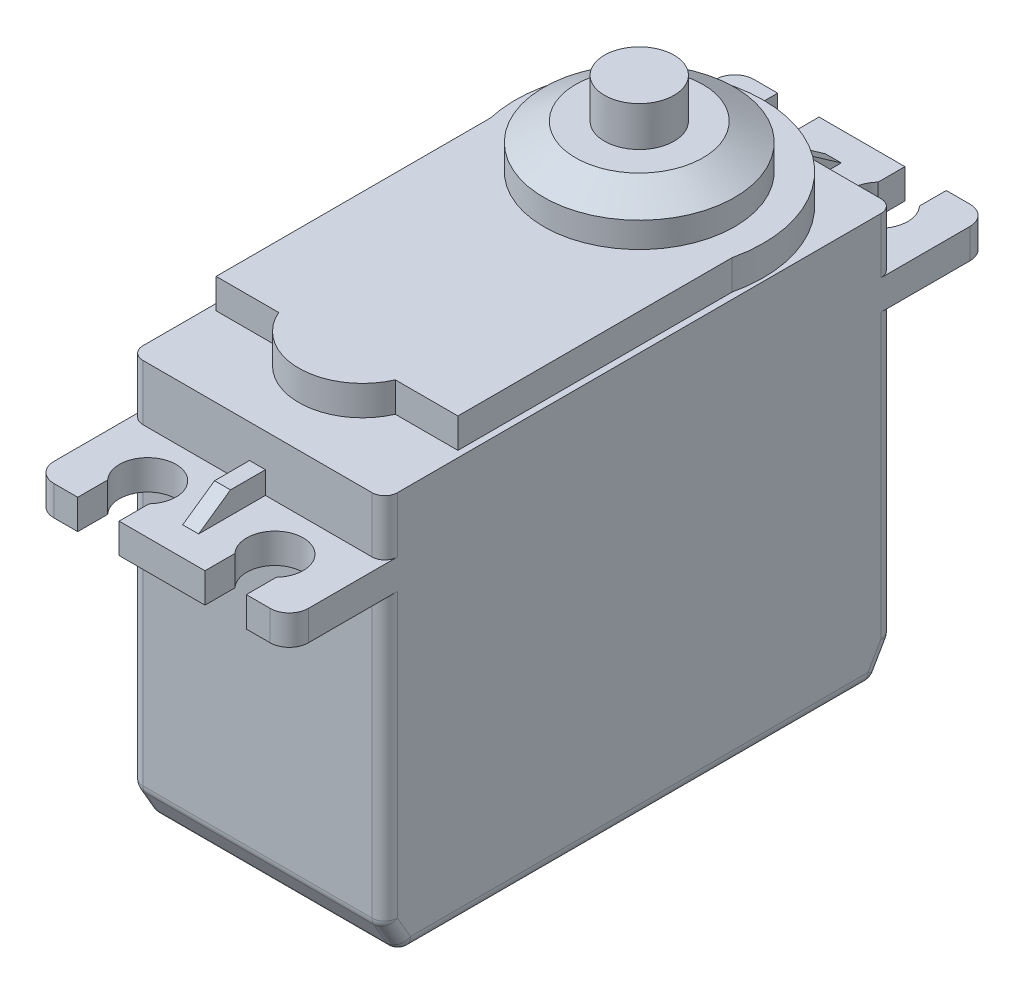
SolidWorks part; units mm, degrees
ref_plane "Front Plane" through (0, 0, 0) normal (0, 0, 1) x (1, 0, 0)
ref_plane "Top Plane" through (0, 0, 0) normal (0, 1, 0) x (1, 0, 0)
ref_plane "Right Plane" through (0, 0, 0) normal (1, 0, 0) x (0, 0, -1)
sketch "Sketch1" plane through (0, 0, 0) normal (0, 1, 0) x (1, 0, 0)
  line L1 (-10.16, 10.16) -> (10.16, 10.16)
  line L2 (-10.16, 10.16) -> (-10.16, -30.48)
  line L3 (-10.16, -30.48) -> (10.16, -30.48)
  line L4 (10.16, 10.16) -> (10.16, -30.48)
  dimension "D1" = 20.32
  dimension "D2" = 40.64
  dimension "D3" = 10.16
  dimension "D4" = 10.16
extrude "Extrude1" add sketch "Sketch1" along normal blind 25.4
sketch "Sketch2" plane through (0, 25.4, 0) normal (0, 1, 0) x (-1, 0, 0)
  line L0 (10.16, 30.48) -> (10.16, 38.1)
  line L1 (10.16, 38.1) -> (6.731, 38.1)
  line L2 (-10.16, 38.1) -> (-10.16, 30.48)
  line L3 (10.16, -10.16) -> (10.16, -17.78)
  line L4 (10.16, -10.16) -> (10.16, 30.48)
  line L5 (10.16, 30.48) -> (-10.16, 30.48)
  line L6 (-10.16, 30.48) -> (-10.16, -10.16)
  line L7 (-10.16, -10.16) -> (10.16, -10.16)
  line L8 (10.16, -10.16) -> (10.16, 30.48)
  line L9 (10.16, 30.48) -> (-10.16, 30.48)
  line L10 (-10.16, 30.48) -> (-10.16, -10.16)
  line L11 (-10.16, -10.16) -> (10.16, -10.16)
  line L12 (10.16, -17.78) -> (6.731, -17.78)
  line L13 (-10.16, -17.78) -> (-10.16, -10.16)
  line L14 (-6.731, 35.7072) -> (-6.731, 38.1)
  line L15 (-3.429, 35.7072) -> (-3.429, 38.1)
  line L16 (3.429, 35.7072) -> (3.429, 38.1)
  line L17 (6.731, 35.7072) -> (6.731, 38.1)
  line L18 (6.731, -15.6412) -> (6.731, -17.78)
  line L19 (3.429, -15.6412) -> (3.429, -17.78)
  line L20 (-3.429, -15.6412) -> (-3.429, -17.78)
  line L21 (-6.731, -15.6412) -> (-6.731, -17.78)
  line L22 (-6.731, -17.78) -> (-10.16, -17.78)
  line L23 (3.429, -17.78) -> (-3.429, -17.78)
  line L24 (-6.731, 38.1) -> (-10.16, 38.1)
  line L25 (3.429, 38.1) -> (-3.429, 38.1)
  arc A0 (3.429, 35.7072) -> (6.731, 35.7072) centre (5.08, 34.163) ccw
  arc A1 (-6.731, 35.7072) -> (-3.429, 35.7072) centre (-5.08, 34.163) ccw
  arc A2 (-3.429, -15.6412) -> (-6.731, -15.6412) centre (-5.08, -14.097) ccw
  arc A3 (6.731, -15.6412) -> (3.429, -15.6412) centre (5.08, -14.097) ccw
  line M5 (10.16, -10.16) -> (10.16, 30.48)
  line M6 (10.16, 30.48) -> (-10.16, 30.48)
  line M7 (-10.16, 30.48) -> (-10.16, -10.16)
  line M8 (-10.16, -10.16) -> (10.16, -10.16)
  dimension "D2" = 4.5212
  dimension "D9" = 3.302
  dimension "D3" = 5.08
  dimension "D4" = 10.16
  dimension "D5" = 48.26
  dimension "D6" = 3.937
  dimension "D7" = 7.62
  dimension "D8" = 7.62
  dimension "D10" = 3.302
  dimension "D11" = 1.651
  dimension "D12" = 1.651
  dimension "D1" = 0
extrude "Extrude2" add sketch "Sketch2" along normal blind 2.3813 contours M8 M5 M6 M7 | A3 L18 L12 L3 L13 L22 L21 A2 L20 L23 L19 M8 | A1 L14 L24 L2 L0 L1 L17 A0 L16 L25 L15 M6
sketch "Sketch3" plane through (0, 27.7812, 0) normal (0, 1, 0) x (-1, 0, 0)
  line L4 (10.16, -10.16) -> (10.16, 30.48)
  line L5 (-10.16, -10.16) -> (10.16, -10.16)
  line L6 (-10.16, 30.48) -> (-10.16, -10.16)
  line L7 (10.16, 30.48) -> (-10.16, 30.48)
  line L8 (10.16, -10.16) -> (10.16, 30.48)
  line L9 (-10.16, -10.16) -> (10.16, -10.16)
  line L10 (-10.16, 30.48) -> (-10.16, -10.16)
  line L11 (10.16, 30.48) -> (-10.16, 30.48)
  dimension "D1" = 0
extrude "Extrude3" add sketch "Sketch3" along normal blind 4.445
sketch "Sketch4" plane through (0, 32.2263, 0) normal (0, 1, 0) x (-1, 0, 0)
  line L0 (9.652, 2.2288) -> (9.652, 24.13)
  line L1 (9.652, 24.13) -> (4.6559, 24.13)
  line L2 (-9.652, 24.13) -> (-9.652, 2.2288)
  line L3 (10.16, 30.48) -> (-10.16, 30.48) construction
  line L4 (-4.6559, 24.13) -> (-9.652, 24.13)
  arc A0 (-9.652, 2.2288) -> (9.652, 2.2288) centre (0, 0) ccw
  arc A1 (4.6559, 24.13) -> (-4.6559, 24.13) centre (0, 22.098) ccw
  dimension "D1" = 19.812
  dimension "D5" = 5.08
  dimension "D2" = 6.35
  dimension "D3" = 19.304
  dimension "D4" = 9.652
  dimension "D6" = 2.032
extrude "Extrude4" add sketch "Sketch4" along normal blind 2.3813
ref_plane "Plane1" through (0, 38.1, 0) normal (0, -1, 0) x (1, 0, 0)
sketch "Sketch5" plane through (0, 34.6075, 0) normal (0, 1, 0) x (-1, 0, 0)
  circle A0 centre (0, 0) radius 7.62
  dimension "D1" = 15.24
extrude "Extrude5" add sketch "Sketch5" along normal up to surface (3.4925 mm away) up to plane "Plane1"
chamfer "Chamfer1" distance 2.54 angle 30 1 edges at (0, 38.1, -7.62)
sketch "Sketch7" plane through (0, 0, 0) normal (1, 0, 0) x (0, 0, -1)
  line L0 (15.494, 27.7812) -> (12.954, 29.5592)
  line L4 (12.954, 29.5592) -> (10.16, 29.5592)
  line L5 (10.16, 32.2263) -> (10.16, 27.7812) construction
  line L6 (17.78, 27.7812) -> (10.16, 27.7812) construction
  line L7 (10.16, 29.5592) -> (10.16, 27.7812)
  line L8 (10.16, 27.7812) -> (15.494, 27.7812)
  dimension "D1" = 1.778
  dimension "D2" = 2.794
  dimension "D3" = 5.334
extrude "Extrude6" add sketch "Sketch7" along normal mid plane 1.27
ref_plane "Plane2" through (0, 0, 10.16) normal (0, 0, -1) x (-1, 0, 0)
mirror "Mirror1" about plane through (0, 0, 10.16) normal (0, 0, -1) of "Extrude6"
sketch "Sketch8" plane through (0, 38.1, 0) normal (0, 1, 0) x (-1, 0, 0)
  circle A0 centre (0, 0) radius 2.7781
  dimension "D1" = 5.5562
extrude "Extrude7" add sketch "Sketch8" along normal blind 3.175
chamfer "Chamfer2" distance 2.54 angle 30 2 edges at (0, 0, 30.48) (0, 0, -10.16)
fillet "Fillet1" radius 1.016 18 edges at (10.16, 0, 10.16) (10.16, 1.27, -9.4268) (0, 0, -8.6935) (0, 2.54, -10.16) (-10.16, 1.27, -9.4268) (10.16, 1.27, 29.7468) (0, 2.54, 30.48) (-10.16, 0, 10.16) (0, 0, 29.0135) (-10.16, 1.27, 29.7468)
fillet "Fillet2" radius 1.524 4 edges at (-10.16, 26.5906, 38.1) (10.16, 26.5906, 38.1) (-10.16, 26.5906, -17.78) (10.16, 26.5906, -17.78)
sketch "Sketch9" plane through (0, 0, -10.16) normal (0, 0, -1) x (-1, 0, 0)
  line L1 (-3.175, 5.588) -> (3.175, 5.588)
  line L2 (-3.175, 5.588) -> (-3.175, 3.048)
  line L3 (-3.175, 3.048) -> (3.175, 3.048)
  line L4 (3.175, 5.588) -> (3.175, 3.048)
  dimension "D1" = 6.35
  dimension "D2" = 2.54
  dimension "D3" = 3.048
  dimension "D4" = 3.175
extrude "Extrude8" add sketch "Sketch9" along normal blind 2.3813
sketch "Sketch10" plane through (0, 0, -12.5412) normal (0, 0, -1) x (-1, 0, 0)
  line L8 (-2.54, 4.953) -> (-2.54, 3.683)
  line L9 (-2.54, 3.683) -> (2.54, 3.683)
  line L10 (2.54, 3.683) -> (2.54, 4.953)
  line L11 (2.54, 4.953) -> (-2.54, 4.953)
  line L12 (-2.54, 4.953) -> (-2.54, 3.683)
  line L13 (-2.54, 3.683) -> (2.54, 3.683)
  line L14 (2.54, 3.683) -> (2.54, 4.953)
  line L15 (2.54, 4.953) -> (-2.54, 4.953)
  dimension "D1" = 0.635
extrude "Cut-Extrude1" cut sketch "Sketch10" against normal up to surface (2.3813 mm away) up to face at (2.286, 14.1061, -10.16)
